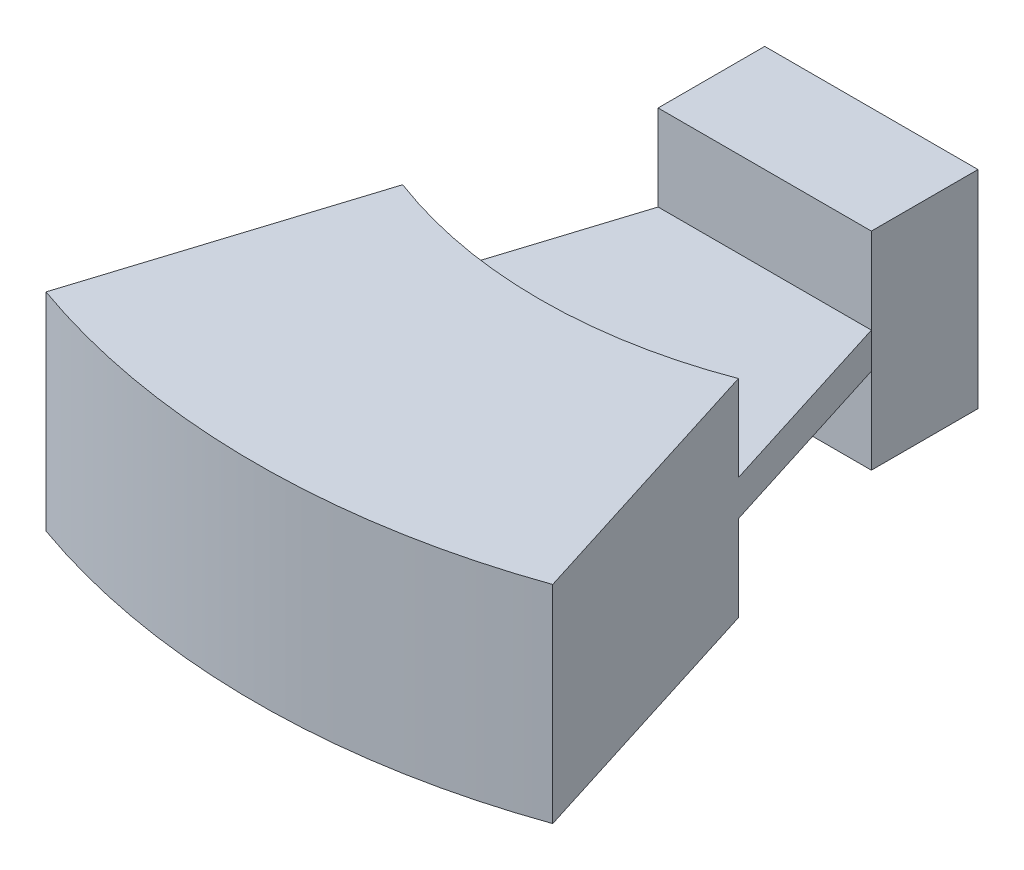
SolidWorks part; units mm, degrees
ref_plane "Front Plane" through (0, 0, 0) normal (0, 0, 1) x (1, 0, 0)
ref_plane "Top Plane" through (0, 0, 0) normal (0, 1, 0) x (1, 0, 0)
ref_plane "Right Plane" through (0, 0, 0) normal (1, 0, 0) x (0, 0, -1)
sketch "Sketch1" plane through (0, 0, 0) normal (0, 1, 0) x (1, 0, 0)
  line L0 (0, 0) -> (0, 30.2699) construction
  line L2 (-19.05, -25.4) -> (19.05, -25.4)
  line L3 (-19.05, -25.4) -> (-19.05, -44.45)
  line L4 (-19.05, -44.45) -> (19.05, -44.45)
  line L5 (19.05, -25.4) -> (19.05, -44.45)
  dimension "D1" = 38.1
  dimension "D2" = 25.4
  dimension "D3" = 19.05
extrude "Boss-Extrude1" add sketch "Sketch1" along normal mid plane 37
sketch "Sketch2" plane through (0, 0, 0) normal (0, 1, 0) x (1, 0, 0)
  circle A0 centre (0, 0) radius 110 construction
  dimension "D1" = 220
sketch "Sketch4" plane through (0, 0, 0) normal (0, 1, 0) x (1, 0, 0)
  line L0 (-19.05, -44.45) -> (-37.6258, -103.3649)
  line L1 (-19.05, -44.45) -> (19.05, -44.45) construction
  line L2 (37.6258, -103.3649) -> (19.05, -44.45)
  line L3 (-19.05, -44.45) -> (19.05, -44.45)
  line L4 (0, 0) -> (0, -92.3593) construction
  circle A1 centre (0, 0) radius 110 construction
  arc A2 (-37.6258, -103.3649) -> (37.6258, -103.3649) centre (0, 0) ccw
  dimension "D1" = 35
extrude "Boss-Extrude3" add sketch "Sketch4" along normal mid plane 6.35
sketch "Sketch7" plane through (0, 0, 0) normal (0, 1, 0) x (1, 0, 0)
  line L0 (-19.05, -44.45) -> (-37.6258, -103.3649) construction
  line L1 (-29.9879, -79.1405) -> (-45.2637, -127.5893)
  line L2 (37.6258, -103.3649) -> (19.05, -44.45) construction
  line L3 (45.2637, -127.5893) -> (29.9879, -79.1405)
  arc A0 (-29.9879, -79.1405) -> (29.9879, -79.1405) centre (0, 0) ccw
  arc A1 (-45.2637, -127.5893) -> (45.2637, -127.5893) centre (0, 0) ccw
  dimension "D1" = 25.4
  dimension "D2" = 50.8
extrude "Boss-Extrude4" add sketch "Sketch7" along normal mid plane 37
